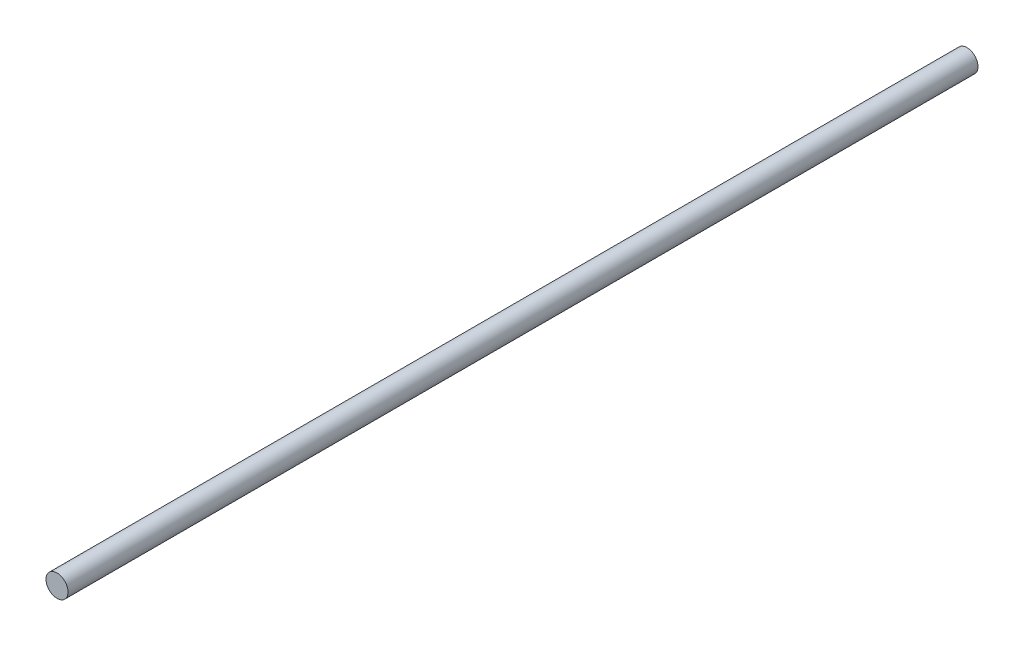
SolidWorks part; units mm, degrees
material "1060 Alloy"
ref_plane "Front Plane" through (0, 0, 0) normal (0, 0, 1) x (1, 0, 0)
ref_plane "Top Plane" through (0, 0, 0) normal (0, 1, 0) x (1, 0, 0)
ref_plane "Right Plane" through (0, 0, 0) normal (1, 0, 0) x (0, 0, -1)
sketch "Sketch1" plane through (0, 0, 0) normal (0, 0, 1) x (1, 0, 0)
  circle A0 centre (0, 0) radius 4
  dimension "D1" = 8
extrude "Boss-Extrude1" add sketch "Sketch1" along normal mid plane 330
